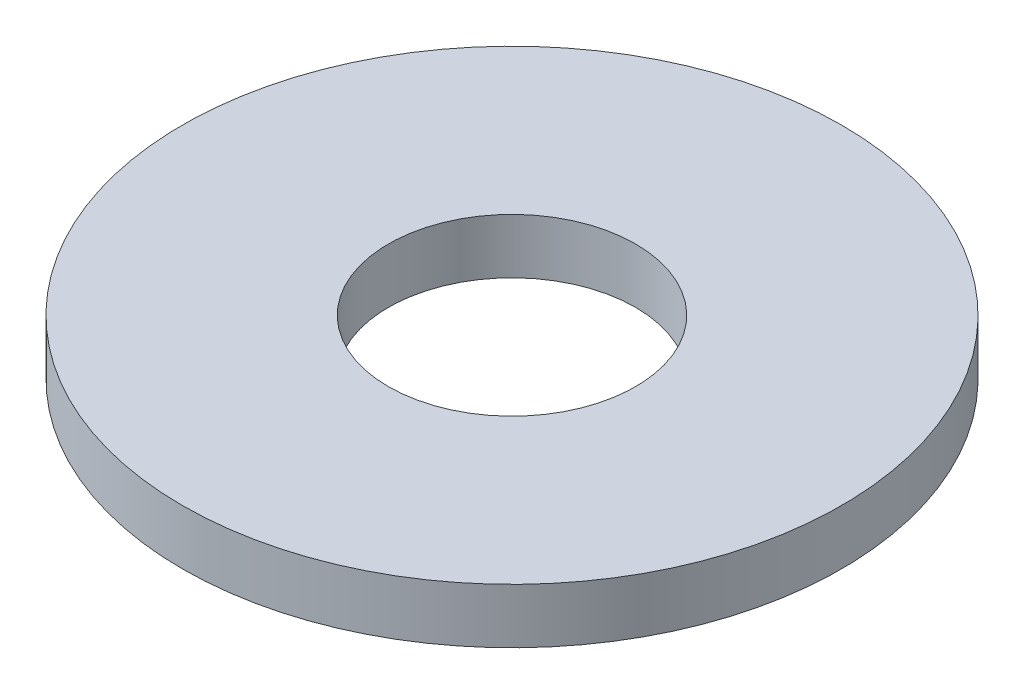
SolidWorks part; units mm, degrees
ref_plane "Спереди" through (0, 0, 0) normal (0, 0, 1) x (1, 0, 0)
ref_plane "Сверху" through (0, 0, 0) normal (0, 1, 0) x (1, 0, 0)
ref_plane "Справа" through (0, 0, 0) normal (1, 0, 0) x (0, 0, -1)
sketch "Эскиз1" plane through (0, 0, 0) normal (0, 1, 0) x (1, 0, 0)
  circle A0 centre (0, 0) radius 6
  circle A1 centre (0, 0) radius 2.25
  dimension "D1" = 12
  dimension "D2" = 4.5
extrude "Бобышка-Вытянуть1" add sketch "Эскиз1" along normal blind 1
